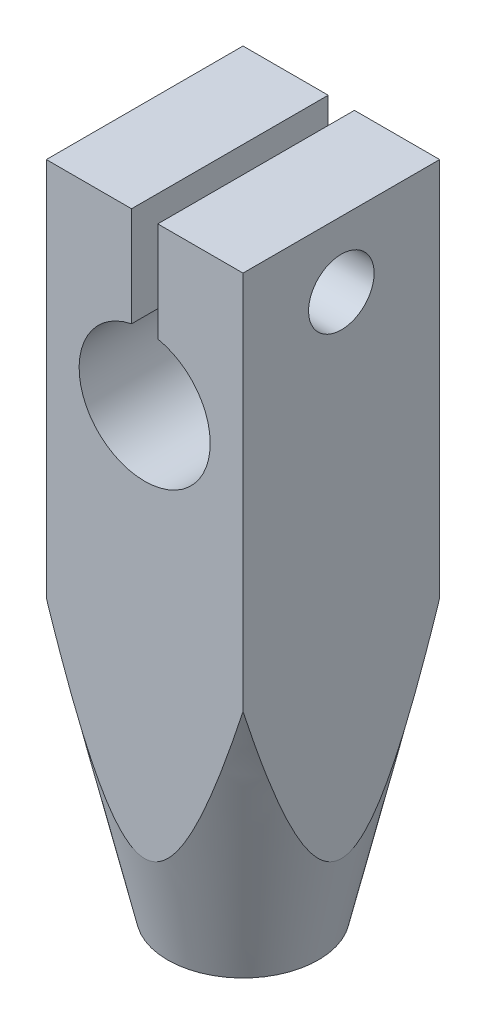
SolidWorks part; units mm, degrees
ref_plane "Front Plane" through (0, 0, 0) normal (0, 0, 1) x (1, 0, 0)
ref_plane "Top Plane" through (0, 0, 0) normal (0, 1, 0) x (1, 0, 0)
ref_plane "Right Plane" through (0, 0, 0) normal (1, 0, 0) x (0, 0, -1)
sketch "Sketch1" plane through (0, 0, 0) normal (0, 0, 1) x (1, 0, 0)
  line L0 (0, 200) -> (0, 183.3974) construction
  line L1 (-3, 205) -> (3, 205)
  line L2 (-3, 205) -> (-3, 185)
  line L3 (-3, 185) -> (3, 185)
  line L4 (3, 205) -> (3, 185)
  circle A0 centre (0, 200) radius 2 construction
  circle A1 centre (0, 200) radius 2
  point P4 (0, 205)
  point P9 (0, 0)
  point P12 (0, 0)
  dimension "D1" = 20
  dimension "D2" = 6
  dimension "D3" = 5
extrude "Boss-Extrude1" add sketch "Sketch1" along normal mid plane 6
sketch "Sketch3" plane through (0, 0, 0) normal (0, 0, 1) x (1, 0, 0)
  line L0 (0, 200) -> (0, 183.3974) construction
  line L4 (-3, 188.032) -> (-3, 185) construction
  line L5 (-3, 185) -> (-2.3, 185)
  line L6 (-3, 185) -> (3, 185) construction
  line L7 (-2.3, 185) -> (-3, 188.032)
  line L8 (-3, 188.032) -> (-6.9174, 205)
  line L9 (-6.9174, 205) -> (-6.9174, 185)
  line L10 (-6.9174, 185) -> (-3, 185)
  point P3 (0, 0)
  point P6 (0, 0)
  point P7 (0, 0)
  point P13 (-5.9529, 197.9921)
  point P14 (0, 0)
  dimension "D1" = 2.3
  dimension "D2" = 77
revolve "Cut-Revolve3" cut sketch "Sketch3" angle 360 about L0
sketch "Sketch4" plane through (0, 185, 0) normal (0, -1, 0) x (1, 0, 0)
  circle A0 centre (0, 0) radius 1.5
  dimension "D1" = 3
extrude "Cut-Extrude1" cut sketch "Sketch4" against normal blind 10
sketch "Sketch5" plane through (0, 0, 3) normal (0, 0, 1) x (1, 0, 0)
  line L0 (3, 205) -> (-3, 205) construction
  line L1 (-0.4, 205) -> (0.4, 205)
  line L2 (-0.4, 205) -> (-0.4, 200.505)
  line L3 (-0.4, 200.505) -> (0.4, 200.505)
  line L4 (0.4, 205) -> (0.4, 200.505)
  point P6 (0, 205)
  point P7 (0, 205)
  point P8 (0, 200.505)
  dimension "D1" = 0.8
extrude "Cut-Extrude2" cut sketch "Sketch5" against normal through all
sketch "Sketch6" plane through (3, 0, 0) normal (1, 0, 0) x (0, 0, -1)
  line L0 (-3, 205) -> (3, 205) construction
  circle A0 centre (0, 203) radius 1
  dimension "D1" = 2
  dimension "D2" = 2
extrude "Cut-Extrude3" cut sketch "Sketch6" against normal through all
equation "\"D1@Boss-Extrude1\"=\"D2@Sketch1\""
